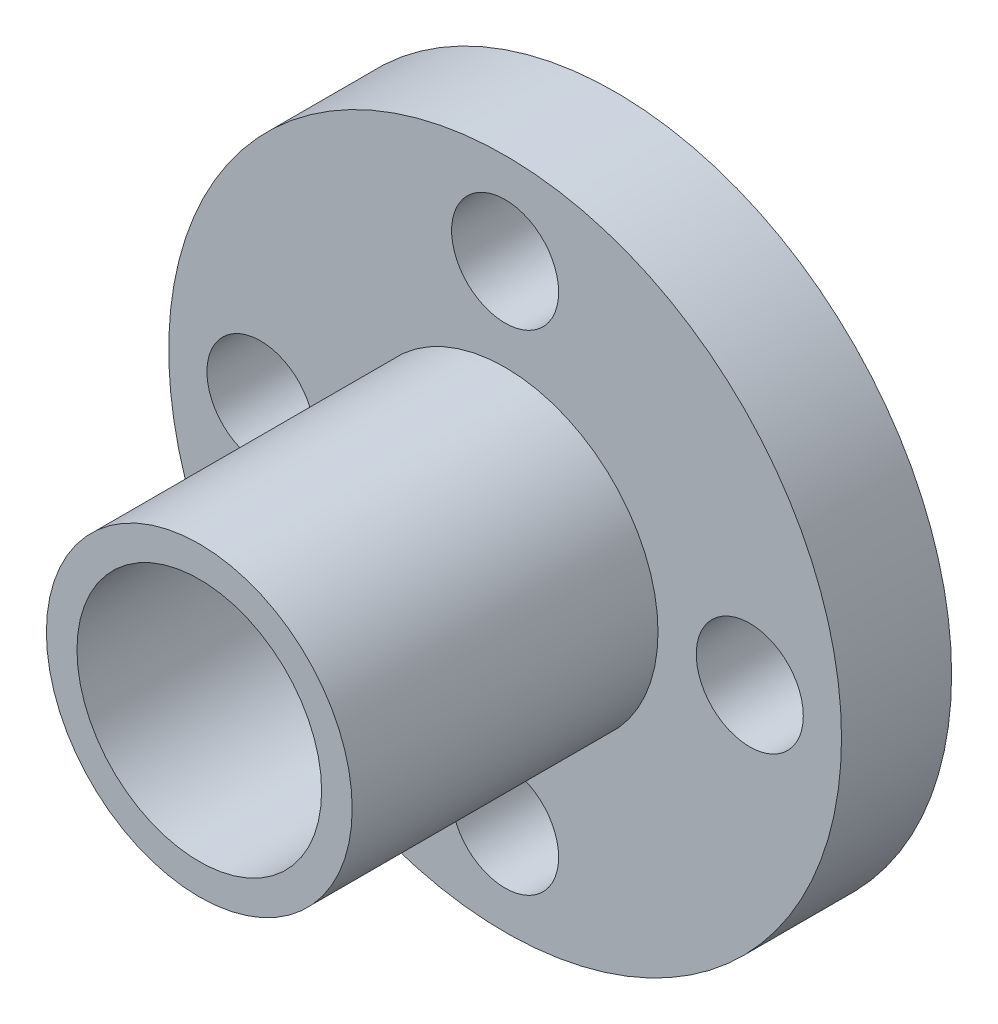
SolidWorks part; units mm, degrees
ref_plane "Спереди" through (0, 0, 0) normal (0, 0, 1) x (1, 0, 0)
ref_plane "Сверху" through (0, 0, 0) normal (0, 1, 0) x (1, 0, 0)
ref_plane "Справа" through (0, 0, 0) normal (1, 0, 0) x (0, 0, -1)
sketch "Эскиз1" plane through (0, 0, 0) normal (0, 0, 1) x (1, 0, 0)
  line L0 (0, -8) -> (0, 8) construction
  line L1 (8, 0) -> (-8, 0) construction
  line L2 (0, -8) -> (0, -12.0205) construction
  line L3 (8, 0) -> (13.9238, 0) construction
  circle A0 centre (0, 0) radius 11
  circle A1 centre (0, 0) radius 8 construction
  circle A2 centre (0, 8) radius 1.75
  circle A3 centre (8, 0) radius 1.75
  circle A4 centre (0, -8) radius 1.75
  circle A5 centre (-8, 0) radius 1.75
  point P15 (0, 0)
  dimension "D1" = 22
  dimension "D2" = 16
  dimension "D3" = 3.5
  dimension "D4" = 4
extrude "Бобышка-Вытянуть1" add sketch "Эскиз1" along normal blind 3.6
sketch "Эскиз2" plane through (0, 0, 3.6) normal (0, 0, 1) x (1, 0, 0)
  circle A0 centre (0, 0) radius 5
  dimension "D1" = 10
extrude "Вытянуть-Тонкостенный1" add sketch "Эскиз2" along normal blind 10 and the other way blind 5.1 thin thin type one direction reverse wall 1
sketch "Эскиз3" plane through (0, 0, 0) normal (0, 0, -1) x (-1, 0, 0)
  circle A0 centre (0, 0) radius 4
  dimension "D1" = 8
extrude "Вырез-Вытянуть1" cut sketch "Эскиз3" against normal through all
